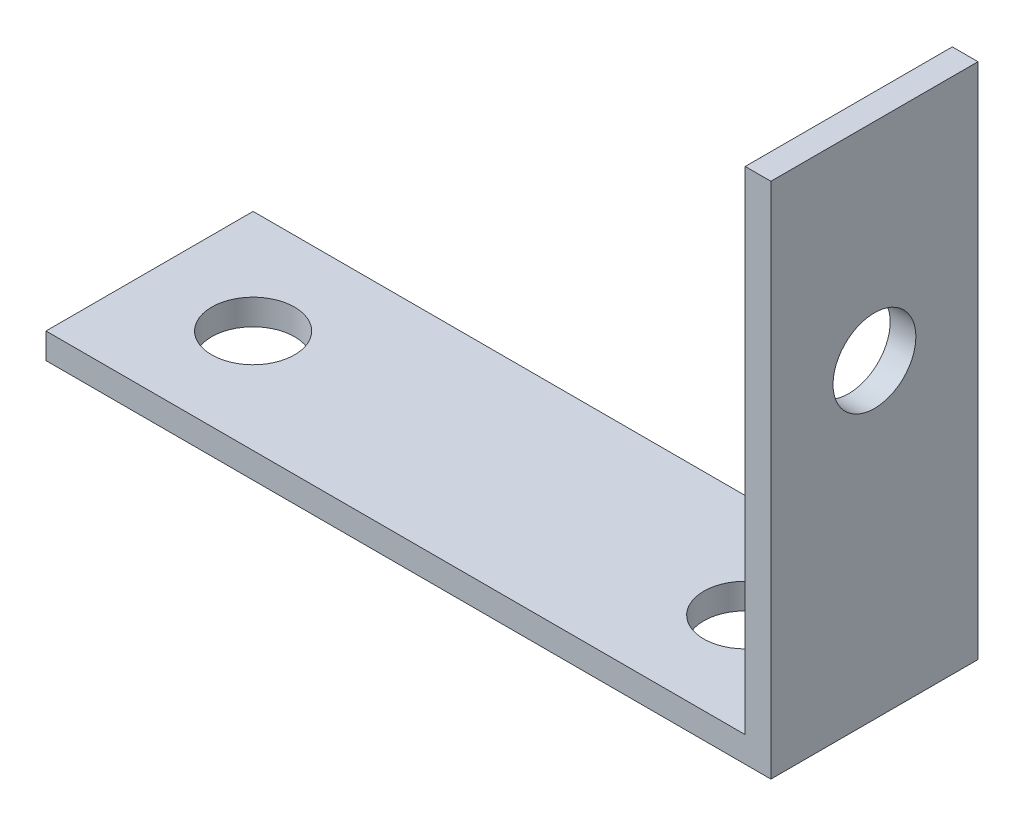
SolidWorks part; units mm, degrees
material "6061 Alloy"
ref_plane "Front Plane" through (0, 0, 0) normal (0, 0, 1) x (1, 0, 0)
ref_plane "Top Plane" through (0, 0, 0) normal (0, 1, 0) x (1, 0, 0)
ref_plane "Right Plane" through (0, 0, 0) normal (1, 0, 0) x (0, 0, -1)
sketch "Sketch1" plane through (0, 0, 0) normal (0, 0, 1) x (1, 0, 0)
  line L0 (0, 0) -> (44.45, 0)
  line L1 (44.45, 0) -> (44.45, 31.75)
  line L2 (44.45, 31.75) -> (42.8752, 31.75)
  line L3 (42.8752, 31.75) -> (42.8752, 1.5748)
  line L4 (42.8752, 1.5748) -> (0, 1.5748)
  line L5 (0, 1.5748) -> (0, 0)
  dimension "D1" = 1.5748
  dimension "D2" = 44.45
  dimension "D3" = 31.75
extrude "Boss-Extrude1" add sketch "Sketch1" along normal blind 12.7
sketch "Sketch2" plane through (42.8752, 0, 0) normal (-1, 0, 0) x (0, 0, 1)
  line L0 (6.35, 31.75) -> (6.35, 1.5748) construction
  line L1 (12.7, 31.75) -> (0, 31.75) construction
  line L2 (12.7, 1.5748) -> (0, 1.5748) construction
  circle A0 centre (6.35, 19.05) radius 2.54
  dimension "D1" = 5.08
  dimension "D2" = 12.7
extrude "Cut-Extrude1" cut sketch "Sketch2" against normal through all
sketch "Sketch3" plane through (0, 1.5748, 0) normal (0, 1, 0) x (1, 0, 0)
  line L0 (0, -6.35) -> (6.35, -6.35) construction
  line L1 (0, -12.7) -> (0, 0) construction
  line L2 (6.35, -6.35) -> (36.5252, -6.35) construction
  line L3 (36.5252, -6.35) -> (42.8752, -6.35) construction
  line L4 (42.8752, -12.7) -> (42.8752, 0) construction
  circle A0 centre (6.35, -6.35) radius 2.54
  circle A1 centre (36.5252, -6.35) radius 2.54
  dimension "D1" = 5.08
  dimension "D2" = 6.35
extrude "Cut-Extrude2" cut sketch "Sketch3" against normal through all
equation "\"base length\" = 21"
equation "\"glass pane length\" = 14.125"
equation "\"glass pane width\" = 10.1875"
equation "\"glass pane wall width\" = 3/4"
equation "\"glass lip\" = 1/4"
equation "\"bolt diameter\" = 0.2"
equation "\"stepper body width\" = 2.22"
equation "\"stepper mount offset\" = 0.19"
equation "\"stepper mount diameter\" = 0.19"
equation "\"stepper shaft offset from body\" = 0.79"
equation "\"stepper spacer thickness\" = 0.2"
equation "\"y axis stepper wall height off base\" = 8"
equation "\"y axis stepper wall bracket thickness\" = 1"
equation "\"y axis stepper wall mount side offset\" = 1/2"
equation "\"y axis stepper wall mount top offset\" = 1/2"
equation "\"y axis stepper wall width\" = \"stepper body width\" + 1                  "
equation "\"y axis bracket height to hole\"= 3.5"
equation "\"thin metal\" = 0.12"
equation "\"thick metal\" = 0.25"
equation "\"foot diameter\"= 0.2"
equation "\"foot inset from corner\"= 1"
equation "\"recognizer width\" = 2.5"
equation "\"recognizer nut plate height\" = 1.25"
equation "\"recognizer nut plate offset\" = 1.5"
equation "\"D1@Sketch2\"=\"bolt diameter\""
equation "\"D1@Sketch3\"=\"bolt diameter\""
equation "\"D3@Sketch1\"=\"recognizer nut plate height\""
